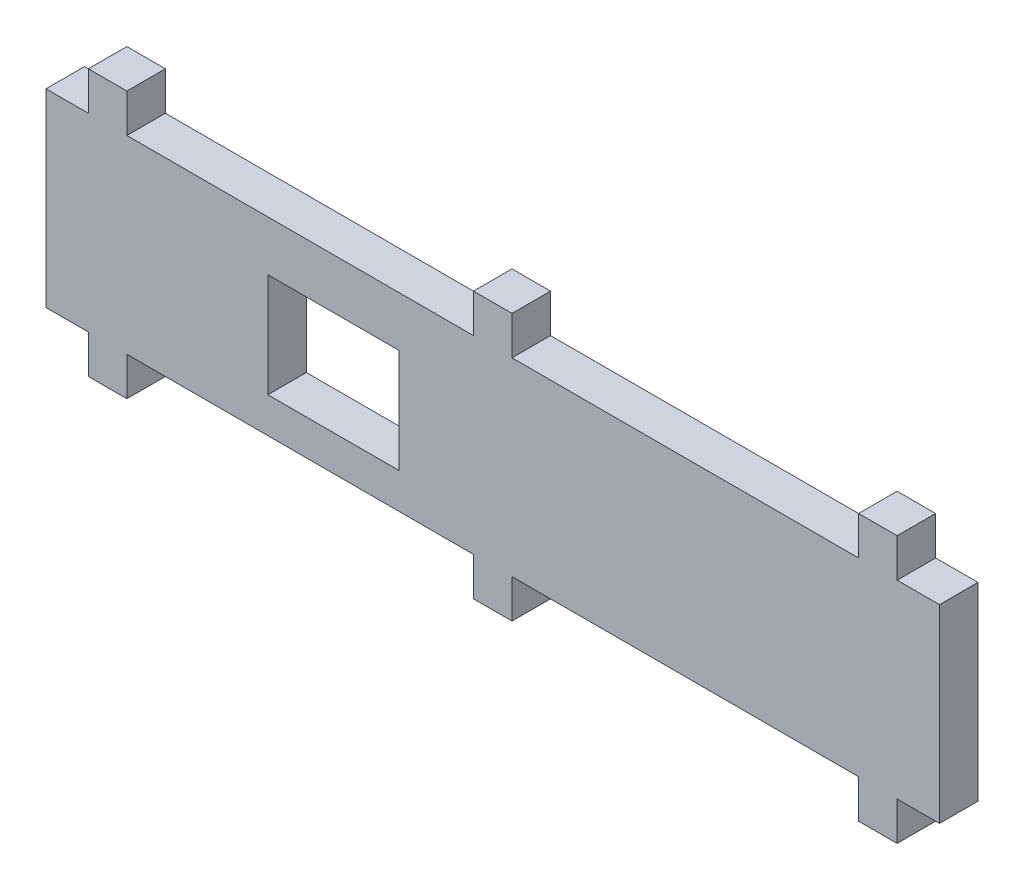
SolidWorks part; units mm, degrees
ref_plane "Front" through (0, 0, 0) normal (0, 0, 1) x (1, 0, 0)
ref_plane "Top" through (0, 0, 0) normal (0, 1, 0) x (1, 0, 0)
ref_plane "Right" through (0, 0, 0) normal (1, 0, 0) x (0, 0, -1)
sketch "Sketch1" plane through (0, 0, 0) normal (0, 0, 1) x (1, 0, 0)
  line L1 (-58, -6.15) -> (58, -6.15)
  line L2 (-58, -6.15) -> (-58, 6.15)
  line L3 (-58, 6.15) -> (58, 6.15)
  line L4 (58, -6.15) -> (58, 6.15)
  line L5 (-58, -6.15) -> (58, 6.15) construction
  line L6 (-58, 6.15) -> (58, -6.15) construction
  point P0 (0, 0)
  dimension "D1" = 12.3
  dimension "D2" = 116
extrude "Boss-Extrude1" add sketch "Sketch1" along normal blind 5
sketch "Sketch2" plane through (0, -6.15, 0) normal (0, -1, 0) x (1, 0, 0)
  line L0 (-58, 5) -> (58, 5) construction
  line L1 (-52.5, 5) -> (-47.5, 5)
  line L2 (-52.5, 5) -> (-52.5, 0)
  line L3 (-52.5, 0) -> (-47.5, 0)
  line L4 (-47.5, 5) -> (-47.5, 0)
  line L5 (-58, 0) -> (58, 0) construction
  line L6 (-58, 5) -> (-58, 0) construction
  line L7 (-2.5, 5) -> (2.5, 5)
  line L8 (-2.5, 5) -> (-2.5, 0)
  line L9 (-2.5, 0) -> (2.5, 0)
  line L10 (2.5, 5) -> (2.5, 0)
  line L11 (47.5, 5) -> (52.5, 5)
  line L12 (47.5, 5) -> (47.5, 0)
  line L13 (47.5, 0) -> (52.5, 0)
  line L14 (52.5, 5) -> (52.5, 0)
  point P16 (-58, 2.5)
  dimension "D1" = 5
  dimension "D2" = 5
  dimension "D3" = 5
  dimension "D4" = 45
  dimension "D5" = 95
  dimension "D6" = 5.5
extrude "Boss-Extrude2" add sketch "Sketch2" along normal blind 5
mirror "Mirror1" about plane through (-58, 6.15, 5) normal (0, -1, 0) of bodies 102
sketch "Sketch3" plane through (0, 0, 5) normal (0, 0, 1) x (1, 0, 0)
  line L0 (-58, 18.45) -> (-58, -6.15) construction
  line L1 (-29.2, -1.55) -> (-12.2, -1.55)
  line L2 (-29.2, -1.55) -> (-29.2, 11.95)
  line L3 (-29.2, 11.95) -> (-12.2, 11.95)
  line L4 (-12.2, -1.55) -> (-12.2, 11.95)
  line L5 (-47.5, -6.15) -> (-2.5, -6.15) construction
  dimension "D1" = 28.8
  dimension "D2" = 17
  dimension "D3" = 4.6
  dimension "D4" = 13.5
extrude "Cut-Extrude1" cut sketch "Sketch3" against normal through all
